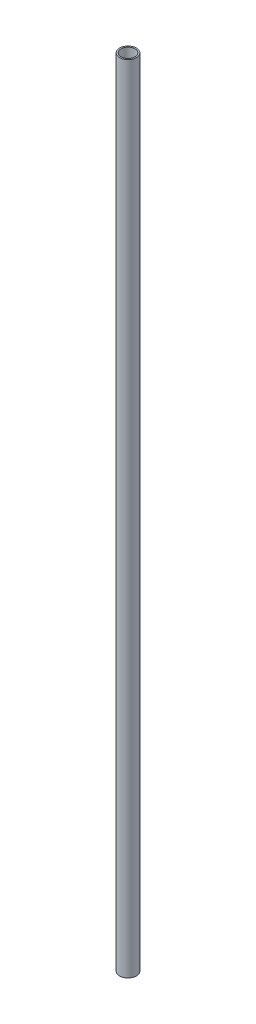
SolidWorks part; units mm, degrees
ref_plane "Front Plane" through (0, 0, 0) normal (0, 0, 1) x (1, 0, 0)
ref_plane "Top Plane" through (0, 0, 0) normal (0, 1, 0) x (1, 0, 0)
ref_plane "Right Plane" through (0, 0, 0) normal (1, 0, 0) x (0, 0, -1)
sketch "Sketch1" plane through (0, 0, 0) normal (0, 1, 0) x (1, 0, 0)
  circle A0 centre (0, 0) radius 3
  circle A1 centre (0, 0) radius 2.5
  dimension "D1" = 6
  dimension "D2" = 5
extrude "Boss-Extrude1" add sketch "Sketch1" along normal blind 285 contours A0 | A1
